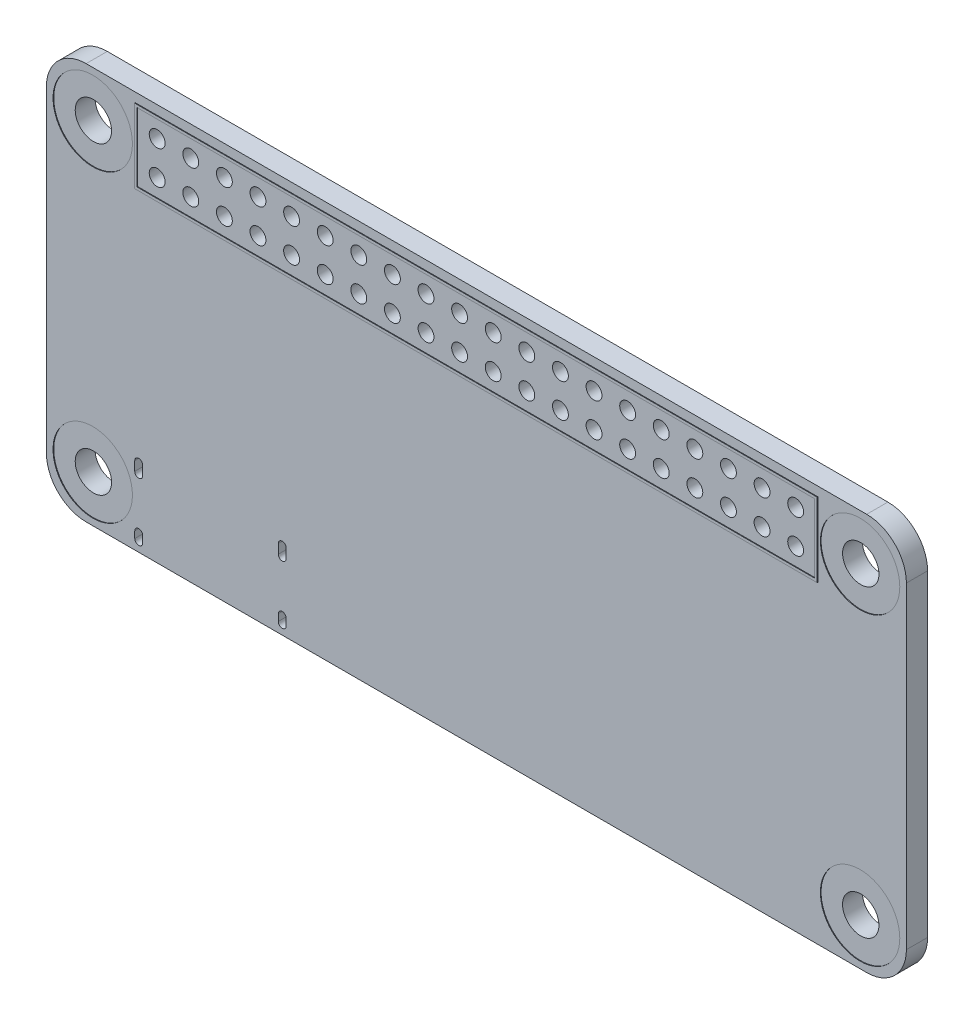
SolidWorks part; units mm, degrees
ref_plane "Front Plane" through (0, 0, 0) normal (0, 0, 1) x (1, 0, 0)
ref_plane "Top Plane" through (0, 0, 0) normal (0, 1, 0) x (1, 0, 0)
ref_plane "Right Plane" through (0, 0, 0) normal (1, 0, 0) x (0, 0, -1)
sketch "Sketch1" plane through (0, 0, 0) normal (0, 0, 1) x (1, 0, 0)
  line L1 (-29.5, 15) -> (29.5, 15)
  line L2 (-32.5, 12) -> (-32.5, -12)
  line L3 (-29.5, -15) -> (29.5, -15)
  line L4 (32.5, 12) -> (32.5, -12)
  line L5 (-32.5, 15) -> (32.5, -15) construction
  line L6 (-32.5, -15) -> (32.5, 15) construction
  line L7 (-29, -11.5) -> (29, -11.5) construction
  line L8 (-29, -11.5) -> (-29, 11.5) construction
  line L9 (-29, 11.5) -> (29, 11.5) construction
  line L10 (29, -11.5) -> (29, 11.5) construction
  line L11 (-29, -11.5) -> (29, 11.5) construction
  line L12 (-29, 11.5) -> (29, -11.5) construction
  arc A0 (29.5, 15) -> (32.5, 12) centre (29.5, 12) cw
  arc A1 (29.5, -15) -> (32.5, -12) centre (29.5, -12) ccw
  arc A2 (-32.5, -12) -> (-29.5, -15) centre (-29.5, -12) ccw
  arc A3 (-29.5, 15) -> (-32.5, 12) centre (-29.5, 12) ccw
  circle A4 centre (-29, 11.5) radius 1.375
  circle A5 centre (29, 11.5) radius 1.375
  circle A6 centre (29, -11.5) radius 1.375
  circle A7 centre (-29, -11.5) radius 1.375
  point P0 (0, 0)
  point P18 (0, 0)
  dimension "D1" = 3
  dimension "D6" = 2.75
  dimension "D2" = 65
  dimension "D3" = 30
  dimension "D4" = 3.5
  dimension "D5" = 3.5
extrude "Boss-Extrude1" add sketch "Sketch1" along normal blind 1.6
sketch "Sketch2" plane through (0, 0, 1.6) normal (0, 0, 1) x (1, 0, 0)
  line L1 (-25.6, 14.1) -> (25.6, 14.1)
  line L2 (-25.6, 14.1) -> (-25.6, 8.9)
  line L3 (-25.6, 8.9) -> (25.6, 8.9)
  line L4 (25.6, 14.1) -> (25.6, 8.9)
  line L5 (-25.6, 14.1) -> (25.6, 8.9) construction
  line L6 (-25.6, 8.9) -> (25.6, 14.1) construction
  point P0 (0, 11.5)
  point P5 (-29, 11.5)
  dimension "D1" = 5.2
  dimension "D2" = 51.2
extrude "Extrude-Thin1" add sketch "Sketch2" along normal blind 0.05 separate body thin thin type one direction wall 0.2
sketch "Sketch3" plane through (0, 0, 1.6) normal (0, 0, 1) x (1, 0, 0)
  line L0 (0, 0) -> (0, 50000) construction
  line L1 (-29, 11.5) -> (29, 11.5) construction
  line L2 (-1.27, 12.77) -> (-3.81, 12.77) construction
  circle A0 centre (-1.27, 12.77) radius 0.6
  circle A1 centre (-3.81, 12.77) radius 0.6
  circle A2 centre (-6.35, 12.77) radius 0.6
  circle A3 centre (-8.89, 12.77) radius 0.6
  circle A4 centre (-11.43, 12.77) radius 0.6
  circle A5 centre (-13.97, 12.77) radius 0.6
  circle A6 centre (-16.51, 12.77) radius 0.6
  circle A7 centre (-19.05, 12.77) radius 0.6
  circle A8 centre (-21.59, 12.77) radius 0.6
  circle A9 centre (-24.13, 12.77) radius 0.6
  circle A10 centre (-24.13, 10.23) radius 0.6
  circle A11 centre (-21.59, 10.23) radius 0.6
  circle A12 centre (-19.05, 10.23) radius 0.6
  circle A13 centre (-16.51, 10.23) radius 0.6
  circle A14 centre (-13.97, 10.23) radius 0.6
  circle A15 centre (-11.43, 10.23) radius 0.6
  circle A16 centre (-8.89, 10.23) radius 0.6
  circle A17 centre (-6.35, 10.23) radius 0.6
  circle A18 centre (-3.81, 10.23) radius 0.6
  circle A19 centre (-1.27, 10.23) radius 0.6
  circle A20 centre (24.13, 10.23) radius 0.6
  circle A21 centre (24.13, 12.77) radius 0.6
  circle A22 centre (21.59, 12.77) radius 0.6
  circle A23 centre (21.59, 10.23) radius 0.6
  circle A24 centre (19.05, 10.23) radius 0.6
  circle A25 centre (19.05, 12.77) radius 0.6
  circle A26 centre (16.51, 12.77) radius 0.6
  circle A27 centre (16.51, 10.23) radius 0.6
  circle A28 centre (13.97, 10.23) radius 0.6
  circle A29 centre (13.97, 12.77) radius 0.6
  circle A30 centre (11.43, 12.77) radius 0.6
  circle A31 centre (11.43, 10.23) radius 0.6
  circle A32 centre (8.89, 10.23) radius 0.6
  circle A33 centre (8.89, 12.77) radius 0.6
  circle A34 centre (6.35, 12.77) radius 0.6
  circle A35 centre (6.35, 10.23) radius 0.6
  circle A36 centre (3.81, 10.23) radius 0.6
  circle A37 centre (3.81, 12.77) radius 0.6
  circle A38 centre (1.27, 12.77) radius 0.6
  circle A39 centre (1.27, 10.23) radius 0.6
  dimension "D1" = 1.2
  dimension "D2" = 1.27
  dimension "D3" = 1.27
  dimension "D5" = 2.54
  dimension "D4" = 10
extrude "Cut-Extrude1" cut sketch "Sketch3" against normal up to next (1.6 mm away)
sketch "Sketch4" plane through (0, 0, 1.6) normal (0, 0, 1) x (1, 0, 0)
  circle A0 centre (-29, 11.5) radius 3
  circle A1 centre (-29, -11.5) radius 3
  circle A2 centre (29, -11.5) radius 3
  circle A3 centre (29, 11.5) radius 3
  dimension "D1" = 6
extrude "Cut-Extrude2" cut sketch "Sketch4" against normal blind 0.05
sketch "Sketch5" plane through (0, 0, 0) normal (0, 0, -1) x (-1, 0, 0)
  circle A0 centre (-29, 11.5) radius 3
  circle A1 centre (-29, -11.5) radius 3
  circle A2 centre (29, -11.5) radius 3
  circle A3 centre (29, 11.5) radius 3
  dimension "D1" = 6
extrude "Cut-Extrude3" cut sketch "Sketch5" against normal blind 0.05
sketch "Sketch6" plane through (0, 0, 0) normal (0, 0, -1) x (-1, 0, 0)
  line L0 (14.675, -9.15) -> (14.675, -9.85) construction
  line L1 (14.975, -9.15) -> (14.975, -9.85)
  line L2 (14.375, -9.15) -> (14.375, -9.85)
  line L3 (14.675, -13.75) -> (14.675, -14.25) construction
  line L4 (14.975, -13.75) -> (14.975, -14.25)
  line L5 (14.375, -13.75) -> (14.375, -14.25)
  line L6 (25.525, -9.15) -> (25.525, -9.85) construction
  line L7 (25.825, -9.15) -> (25.825, -9.85)
  line L8 (25.225, -9.15) -> (25.225, -9.85)
  line L9 (25.525, -13.75) -> (25.525, -14.25) construction
  line L10 (25.825, -13.75) -> (25.825, -14.25)
  line L11 (25.225, -13.75) -> (25.225, -14.25)
  line L12 (32.5, 12) -> (32.5, -12) construction
  line L13 (14.675, -9.5) -> (25.525, -9.5) construction
  line L14 (29.5, -15) -> (-29.5, -15) construction
  line L15 (14.675, -14) -> (25.525, -14) construction
  arc A0 (14.975, -9.15) -> (14.375, -9.15) centre (14.675, -9.15) ccw
  arc A1 (14.375, -9.85) -> (14.975, -9.85) centre (14.675, -9.85) ccw
  arc A2 (14.975, -13.75) -> (14.375, -13.75) centre (14.675, -13.75) ccw
  arc A3 (14.375, -14.25) -> (14.975, -14.25) centre (14.675, -14.25) ccw
  arc A4 (25.825, -9.15) -> (25.225, -9.15) centre (25.525, -9.15) ccw
  arc A5 (25.225, -9.85) -> (25.825, -9.85) centre (25.525, -9.85) ccw
  arc A6 (25.825, -13.75) -> (25.225, -13.75) centre (25.525, -13.75) ccw
  arc A7 (25.225, -14.25) -> (25.825, -14.25) centre (25.525, -14.25) ccw
  point P2 (14.675, -9.5)
  point P7 (14.675, -14)
  point P14 (25.525, -9.5)
  point P21 (25.525, -14)
  point P29 (20.1, -15)
  point P33 (20.1, -9.5)
  point P34 (14.675, -13.3781)
  point P38 (14.675, -8.85)
  point P39 (14.675, -10.15)
  point P41 (14.675, -14)
  point P42 (14.675, -14.25)
  point P45 (14.975, -14.25)
  point P46 (25.525, -14.25)
  point P47 (25.525, -9.85)
  point P48 (0, 0)
  dimension "D1" = 12.4
  dimension "D2" = 10.85
  dimension "D3" = 0.6
  dimension "D4" = 0.6
  dimension "D5" = 1.3
  dimension "D6" = 0.5
  dimension "D7" = 5.5
  dimension "D8" = 4.5
extrude "Cut-Extrude4" cut sketch "Sketch6" against normal up to next (1.6 mm away)
